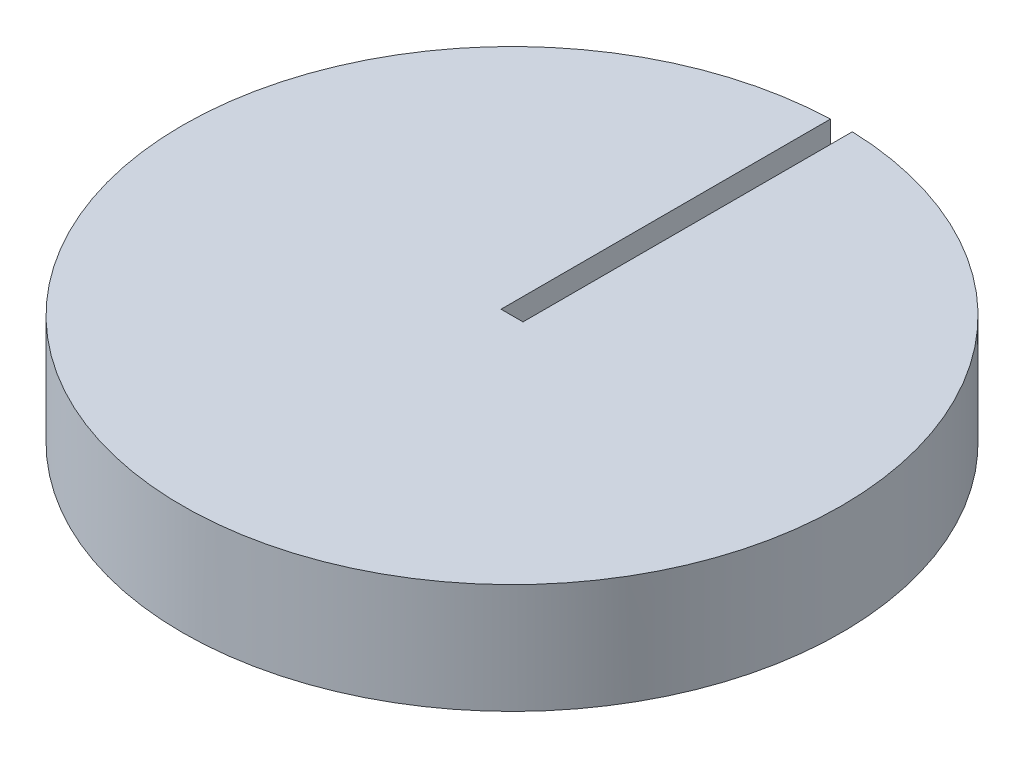
SolidWorks part; units mm, degrees
ref_plane "Front Plane" through (0, 0, 0) normal (0, 0, 1) x (1, 0, 0)
ref_plane "Top Plane" through (0, 0, 0) normal (0, 1, 0) x (1, 0, 0)
ref_plane "Right Plane" through (0, 0, 0) normal (1, 0, 0) x (0, 0, -1)
sketch "Sketch1" plane through (0, 0, 0) normal (0, 1, 0) x (1, 0, 0)
  circle A0 centre (0, 0) radius 38.1
  dimension "D1" = 76.2
extrude "Boss-Extrude1" add sketch "Sketch1" along normal blind 12.7
sketch "Sketch2" plane through (0, 12.7, 0) normal (0, 1, 0) x (1, 0, 0)
  line L0 (0, 0) -> (0, 46.3608)
extrude "Cut-Extrude-Thin2" cut sketch "Sketch2" against normal blind 2.54 thin thin type mid plane wall 2.54
